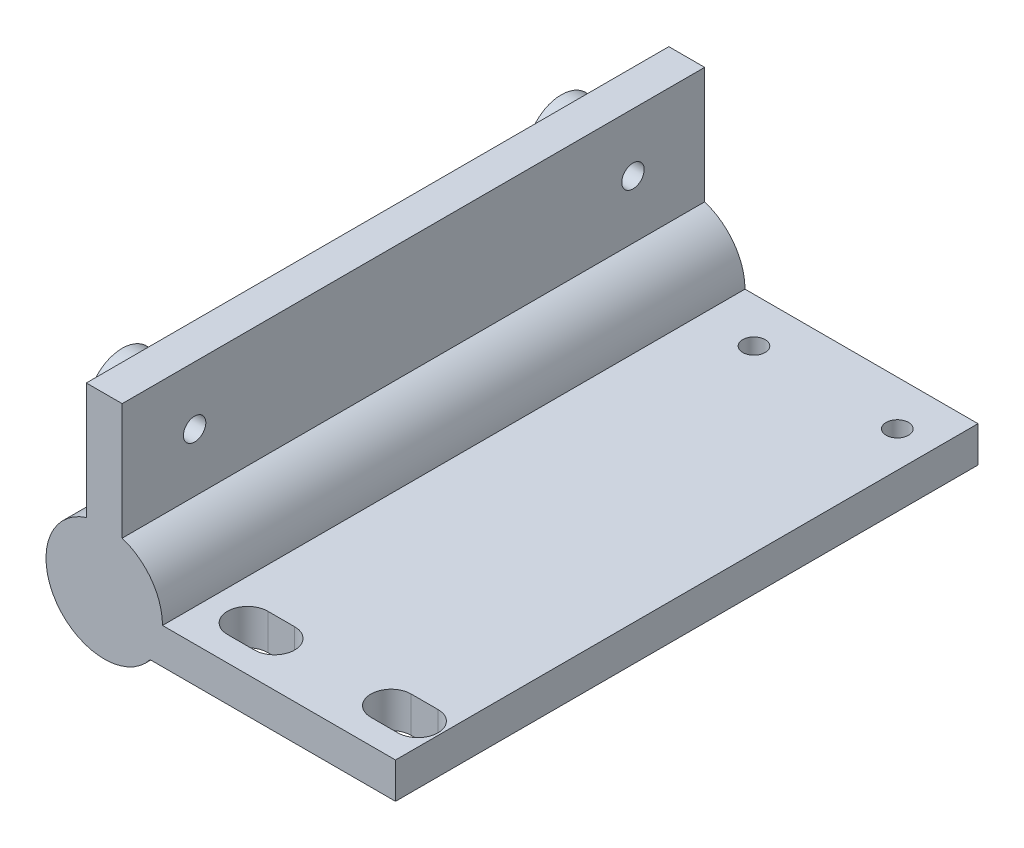
SolidWorks part; units mm, degrees
ref_plane "Спереди" through (0, 0, 0) normal (0, 0, 1) x (1, 0, 0)
ref_plane "Сверху" through (0, 0, 0) normal (0, 1, 0) x (1, 0, 0)
ref_plane "Справа" through (0, 0, 0) normal (1, 0, 0) x (0, 0, -1)
other "Configuration Table"
sketch "Эскиз1" plane through (0, 0, 0) normal (0, 0, 1) x (1, 0, 0)
  line L0 (5.1235, -4) -> (32.5, -4)
  line L1 (32.5, -4) -> (32.5, 0)
  line L2 (32.5, 0) -> (6.5, 0)
  line L4 (-2, 19.1847) -> (2, 19.1847)
  line L5 (-2, 19.1847) -> (-2, 6.1847)
  line L7 (2, 19.1847) -> (2, 6.1847)
  circle A0 centre (0, 0) radius 4.1
  arc A1 (6.5, 0) -> (2, 6.1847) centre (0, 0) ccw
  circle A2 centre (39, 0) radius 6.5 construction
  arc A3 (-2, 6.1847) -> (5.1235, -4) centre (0, 0) ccw
  point P13 (0, 19.1847)
  dimension "D1" = 8.2
  dimension "D2" = 13
  dimension "D3" = 26
  dimension "D7" = 13
  dimension "D4" = 4
  dimension "D5" = 6.5
  dimension "D6" = 32.5
  dimension "D8" = 13
  dimension "D9" = 4
extrude "Бобышка-Вытянуть1" add sketch "Эскиз1" along normal blind 65
sketch "Эскиз2" plane through (0, 0, 65) normal (0, 0, 1) x (1, 0, 0)
  circle A0 centre (0, 0) radius 4.9232
extrude "Бобышка-Вытянуть2" add sketch "Эскиз2" against normal blind 3
sketch "Эскиз3" plane through (0, 0, 0) normal (0, 1, 0) x (1, 0, 0)
  line L0 (32.5, 0) -> (6.5, 0) construction
  line L1 (27, -57.75) -> (30, -57.75)
  line L6 (27, -62.25) -> (30, -62.25)
  line L7 (11, -57.75) -> (14, -57.75)
  line L8 (32.5, -65) -> (6.5, -65) construction
  line L9 (6.5, -65) -> (6.5, 0) construction
  line L10 (11, -62.25) -> (14, -62.25)
  circle A4 centre (12.5, -5) radius 1.25
  circle A5 centre (28.5, -5) radius 1.25
  arc A6 (27, -57.75) -> (27, -62.25) centre (27, -60) ccw
  arc A7 (30, -62.25) -> (30, -57.75) centre (30, -60) ccw
  arc A8 (11, -57.75) -> (11, -62.25) centre (11, -60) ccw
  arc A9 (14, -62.25) -> (14, -57.75) centre (14, -60) ccw
  point P30 (28.5, -57.75)
  point P37 (12.5, -57.75)
  dimension "D1" = 2.5
  dimension "D2" = 2.5
  dimension "D3" = 60
  dimension "D5" = 5
  dimension "D9" = 2.25
  dimension "D10" = 2.25
  dimension "D12" = 2.25
  dimension "D4" = 6
  dimension "D6" = 16
  dimension "D7" = 4.5
  dimension "D8" = 3
  dimension "D11" = 5
  dimension "D13" = 3
extrude "Вырез-Вытянуть1" cut sketch "Эскиз3" against normal blind 13
ref_plane "Плоскость1" through (17.5, 0, 0) normal (1, 0, 0) x (0, 0, -1)
sketch "Эскиз4" plane through (-2, 0, 0) normal (-1, 0, 0) x (0, 0, 1)
  line L0 (65, 19.1847) -> (0, 19.1847) construction
  line L1 (0, 19.1847) -> (0, 6.1847) construction
  line L2 (65, 19.1847) -> (65, 6.1847) construction
  circle A0 centre (8, 12.6847) radius 3.85
  circle A1 centre (57, 12.6847) radius 3.85
  dimension "D1" = 7.7
  dimension "D2" = 7.7
  dimension "D3" = 6.5
  dimension "D4" = 6.5
  dimension "D5" = 8
  dimension "D6" = 8
extrude "Бобышка-Вытянуть3" add sketch "Эскиз4" along normal blind 4
sketch "Эскиз5" plane through (-6, 0, 0) normal (-1, 0, 0) x (0, 0, 1)
  circle A0 centre (8, 12.6847) radius 1.25
  circle A1 centre (56.9166, 12.6847) radius 1.25
  dimension "D1" = 2.5
  dimension "D2" = 2.5
extrude "Вырез-Вытянуть2" cut sketch "Эскиз5" against normal blind 14
